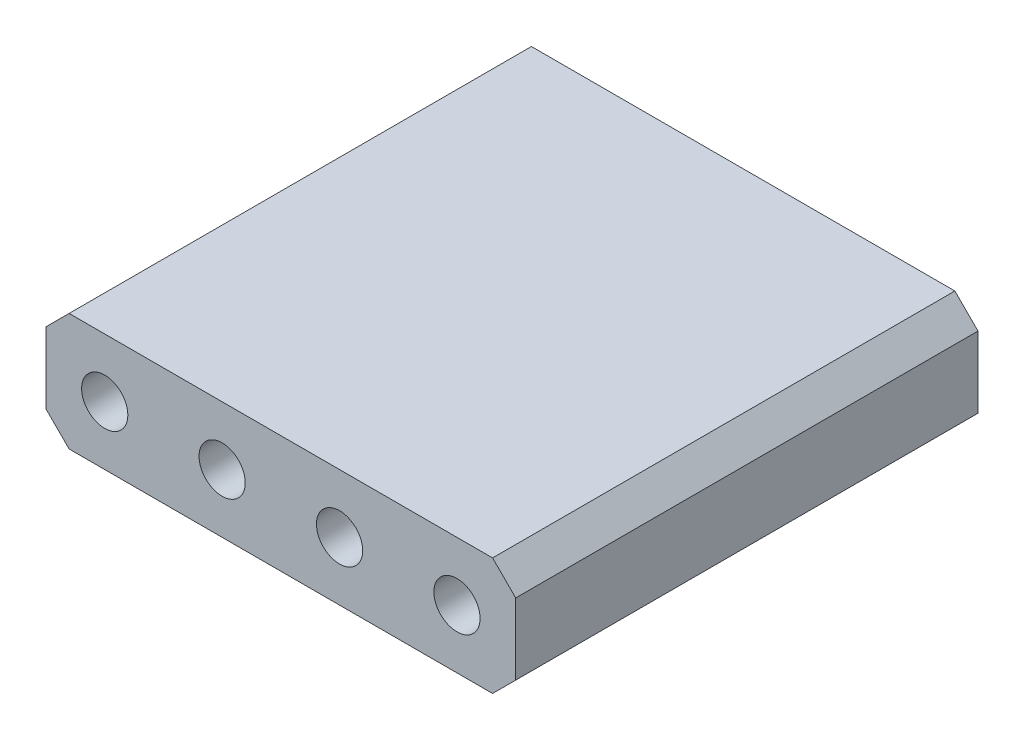
SolidWorks part; units mm, degrees
ref_plane "Спереди" through (0, 0, 0) normal (0, 0, 1) x (1, 0, 0)
ref_plane "Сверху" through (0, 0, 0) normal (0, 1, 0) x (1, 0, 0)
ref_plane "Справа" through (0, 0, 0) normal (1, 0, 0) x (0, 0, -1)
sketch "Эскиз2" plane through (0, 0, 0) normal (0, 0, 1) x (1, 0, 0)
  line L0 (-5.08, 0) -> (5.08, 0) construction
  line L1 (-5.08, -1.27) -> (5.08, -1.27)
  line L2 (-5.08, -1.27) -> (-5.08, 1.27)
  line L3 (-5.08, 1.27) -> (5.08, 1.27)
  line L4 (5.08, -1.27) -> (5.08, 1.27)
  line L5 (-5.08, -1.27) -> (5.08, 1.27) construction
  line L6 (-5.08, 1.27) -> (5.08, -1.27) construction
  circle A4 centre (-3.81, 0) radius 0.5
  circle A5 centre (-1.27, 0) radius 0.5
  circle A6 centre (1.27, 0) radius 0.5
  circle A7 centre (3.81, 0) radius 0.5
  point P0 (0, 0)
  point P16 (0, 0)
  point P18 (-2.2004, -0.0097)
  dimension "D3" = 1.27
  dimension "D1" = 10.16
  dimension "D2" = 2.54
  dimension "D4" = 2.54
  dimension "D5" = 2.54
  dimension "D6" = 2.54
extrude "Бобышка-Вытянуть1" add sketch "Эскиз2" along normal blind 10
chamfer "Фаска2" distance 0.5 angle 45 4 edges at (-5.08, 1.27, 5) (5.08, 1.27, 5) (5.08, -1.27, 5) (-5.08, -1.27, 5)
